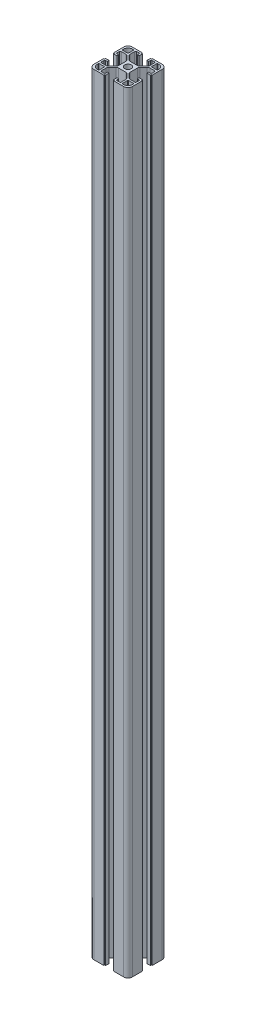
SolidWorks part; units mm, degrees
ref_plane "Front Plane" through (0, 0, 0) normal (0, 0, 1) x (1, 0, 0)
ref_plane "Top Plane" through (0, 0, 0) normal (0, 1, 0) x (1, 0, 0)
ref_plane "Right Plane" through (0, 0, 0) normal (1, 0, 0) x (0, 0, -1)
sketch "Sketch1" plane through (0, 0, 0) normal (0, 1, 0) x (1, 0, 0)
  line L0 (84.1702, 31.7204) -> (84.1702, 42.1204)
  line L1 (44.1702, 62.7204) -> (44.1702, 52.3204)
  line L2 (48.6702, 27.2204) -> (59.0702, 27.2204)
  line L3 (79.6702, 67.2204) -> (69.4702, 67.2204)
  line L4 (84.1702, 52.3204) -> (84.1702, 62.7204)
  line L5 (58.8702, 67.2204) -> (48.6702, 67.2204)
  line L6 (44.1702, 42.1204) -> (44.1702, 31.7204)
  line L7 (69.2702, 27.2204) -> (79.6702, 27.2204)
  line L8 (48.6702, 27.2204) -> (59.0702, 27.2204)
  line L9 (44.1702, 42.1204) -> (44.1702, 31.7204)
  line L10 (44.1702, 42.1204) -> (44.7702, 42.1204)
  line L11 (44.9702, 42.3204) -> (44.9702, 42.9204)
  line L12 (48.6702, 43.1204) -> (45.1702, 43.1204)
  line L13 (48.6702, 41.3204) -> (48.6702, 43.1204)
  line L14 (46.9702, 41.3204) -> (48.6702, 41.3204)
  line L15 (45.9702, 37.9704) -> (45.9702, 40.3204)
  line L16 (51.6169, 36.9704) -> (46.9702, 36.9704)
  line L17 (57.2915, 41.4024) -> (53.7382, 37.8491)
  line L18 (58.1702, 50.9171) -> (58.1702, 43.5237)
  line L19 (53.7382, 56.5917) -> (57.2915, 53.0384)
  line L20 (46.9702, 57.4704) -> (51.6169, 57.4704)
  line L21 (45.9702, 54.1204) -> (45.9702, 56.4704)
  line L22 (48.6702, 53.1204) -> (46.9702, 53.1204)
  line L23 (48.6702, 51.3204) -> (48.6702, 53.1204)
  line L24 (45.1702, 51.3204) -> (48.6702, 51.3204)
  line L25 (44.9702, 51.5204) -> (44.9702, 52.1204)
  line L26 (44.7702, 52.3204) -> (44.1702, 52.3204)
  line L27 (44.1702, 62.7204) -> (44.1702, 52.3204)
  line L28 (58.8702, 67.2204) -> (48.6702, 67.2204)
  line L29 (59.0702, 67.0204) -> (59.0702, 66.6204)
  line L30 (59.2702, 66.4204) -> (59.8702, 66.4204)
  line L31 (60.0702, 62.7204) -> (60.0702, 66.2204)
  line L32 (58.2702, 62.7204) -> (60.0702, 62.7204)
  line L33 (58.2702, 64.4204) -> (58.2702, 62.7204)
  line L34 (54.9202, 65.4204) -> (57.2702, 65.4204)
  line L35 (53.9202, 59.7737) -> (53.9202, 64.4204)
  line L36 (58.3522, 54.0991) -> (54.7989, 57.6524)
  line L37 (67.8669, 53.2204) -> (60.4735, 53.2204)
  line L38 (73.5415, 57.6524) -> (69.9882, 54.0991)
  line L39 (74.4202, 64.4204) -> (74.4202, 59.7737)
  line L40 (71.0702, 65.4204) -> (73.4202, 65.4204)
  line L41 (70.0702, 62.7204) -> (70.0702, 64.4204)
  line L42 (68.2702, 62.7204) -> (70.0702, 62.7204)
  line L43 (68.2702, 66.2204) -> (68.2702, 62.7204)
  line L44 (68.4702, 66.4204) -> (69.0702, 66.4204)
  line L45 (69.2702, 66.6204) -> (69.2702, 67.0204)
  line L46 (79.6702, 67.2204) -> (69.4702, 67.2204)
  line L47 (84.1702, 52.3204) -> (84.1702, 62.7204)
  line L48 (84.1702, 52.3204) -> (83.5702, 52.3204)
  line L49 (83.3702, 52.1204) -> (83.3702, 51.5204)
  line L50 (79.6702, 51.3204) -> (83.1702, 51.3204)
  line L51 (79.6702, 53.1204) -> (79.6702, 51.3204)
  line L52 (81.3702, 53.1204) -> (79.6702, 53.1204)
  line L53 (82.3702, 56.4704) -> (82.3702, 54.1204)
  line L54 (76.7235, 57.4704) -> (81.3702, 57.4704)
  line L55 (71.0489, 53.0384) -> (74.6022, 56.5917)
  line L56 (70.1702, 43.5237) -> (70.1702, 50.9171)
  line L57 (74.6022, 37.8491) -> (71.0489, 41.4024)
  line L58 (81.3702, 36.9704) -> (76.7235, 36.9704)
  line L59 (82.3702, 40.3204) -> (82.3702, 37.9704)
  line L60 (79.6702, 41.3204) -> (81.3702, 41.3204)
  line L61 (79.6702, 43.1204) -> (79.6702, 41.3204)
  line L62 (83.1702, 43.1204) -> (79.6702, 43.1204)
  line L63 (83.3702, 42.9204) -> (83.3702, 42.3204)
  line L64 (83.5702, 42.1204) -> (84.1702, 42.1204)
  line L65 (84.1702, 31.7204) -> (84.1702, 42.1204)
  line L66 (69.2702, 27.2204) -> (79.6702, 27.2204)
  line L67 (69.2702, 27.2204) -> (69.2702, 27.8204)
  line L68 (69.0702, 28.0204) -> (68.4702, 28.0204)
  line L69 (68.2702, 31.7204) -> (68.2702, 28.2204)
  line L70 (70.0702, 31.7204) -> (68.2702, 31.7204)
  line L71 (70.0702, 30.0204) -> (70.0702, 31.7204)
  line L72 (73.4202, 29.0204) -> (71.0702, 29.0204)
  line L73 (74.4202, 34.6671) -> (74.4202, 30.0204)
  line L74 (69.9882, 40.3417) -> (73.5415, 36.7884)
  line L75 (60.4735, 41.2204) -> (67.8669, 41.2204)
  line L76 (54.7989, 36.7884) -> (58.3522, 40.3417)
  line L77 (53.9202, 30.0204) -> (53.9202, 34.6671)
  line L78 (57.2702, 29.0204) -> (54.9202, 29.0204)
  line L79 (58.2702, 31.7204) -> (58.2702, 30.0204)
  line L80 (60.0702, 31.7204) -> (58.2702, 31.7204)
  line L81 (60.0702, 28.2204) -> (60.0702, 31.7204)
  line L82 (59.8702, 28.0204) -> (59.2702, 28.0204)
  line L83 (59.0702, 27.8204) -> (59.0702, 27.2204)
  line L84 (82.3702, 34.6704) -> (82.3702, 33.5204)
  line L85 (76.7202, 35.1704) -> (81.8702, 35.1704)
  line L86 (76.2202, 29.5204) -> (76.2202, 34.6704)
  line L87 (77.8702, 29.0204) -> (76.7202, 29.0204)
  line L88 (51.6202, 29.0204) -> (50.4702, 29.0204)
  line L89 (52.1202, 34.6704) -> (52.1202, 29.5204)
  line L90 (46.4702, 35.1704) -> (51.6202, 35.1704)
  line L91 (45.9702, 33.5204) -> (45.9702, 34.6704)
  line L92 (45.9702, 59.7704) -> (45.9702, 60.9204)
  line L93 (51.6202, 59.2704) -> (46.4702, 59.2704)
  line L94 (52.1202, 64.9204) -> (52.1202, 59.7704)
  line L95 (50.4702, 65.4204) -> (51.6202, 65.4204)
  line L96 (76.7202, 65.4204) -> (77.8702, 65.4204)
  line L97 (76.2202, 59.7704) -> (76.2202, 64.9204)
  line L98 (81.8702, 59.2704) -> (76.7202, 59.2704)
  line L99 (82.3702, 60.9204) -> (82.3702, 59.7704)
  line L100 (71.0702, 65.4204) -> (73.4202, 65.4204)
  line L101 (70.0702, 62.7204) -> (70.0702, 64.4204)
  line L102 (68.2702, 62.7204) -> (70.0702, 62.7204)
  line L103 (68.2702, 66.2204) -> (68.2702, 62.7204)
  line L104 (60.0702, 62.7204) -> (60.0702, 66.2204)
  line L105 (58.2702, 62.7204) -> (60.0702, 62.7204)
  line L106 (58.2702, 64.4204) -> (58.2702, 62.7204)
  line L107 (54.9202, 65.4204) -> (57.2702, 65.4204)
  line L108 (53.9202, 59.7737) -> (53.9202, 64.4204)
  line L109 (58.3522, 54.0991) -> (54.7989, 57.6524)
  line L110 (67.8669, 53.2204) -> (60.4735, 53.2204)
  line L111 (73.5415, 57.6524) -> (69.9882, 54.0991)
  line L112 (74.4202, 64.4204) -> (74.4202, 59.7737)
  line L113 (59.2702, 66.4204) -> (59.8702, 66.4204)
  line L114 (59.0702, 67.0204) -> (59.0702, 66.6204)
  line L115 (69.2702, 66.6204) -> (69.2702, 67.0204)
  line L116 (68.4702, 66.4204) -> (69.0702, 66.4204)
  line L117 (82.3702, 40.3204) -> (82.3702, 37.9704)
  line L118 (79.6702, 41.3204) -> (81.3702, 41.3204)
  line L119 (79.6702, 43.1204) -> (79.6702, 41.3204)
  line L120 (83.1702, 43.1204) -> (79.6702, 43.1204)
  line L121 (79.6702, 51.3204) -> (83.1702, 51.3204)
  line L122 (79.6702, 53.1204) -> (79.6702, 51.3204)
  line L123 (81.3702, 53.1204) -> (79.6702, 53.1204)
  line L124 (82.3702, 56.4704) -> (82.3702, 54.1204)
  line L125 (76.7235, 57.4704) -> (81.3702, 57.4704)
  line L126 (71.0489, 53.0384) -> (74.6022, 56.5917)
  line L127 (70.1702, 43.5237) -> (70.1702, 50.9171)
  line L128 (74.6022, 37.8491) -> (71.0489, 41.4024)
  line L129 (81.3702, 36.9704) -> (76.7235, 36.9704)
  line L130 (45.9702, 54.1204) -> (45.9702, 56.4704)
  line L131 (48.6702, 53.1204) -> (46.9702, 53.1204)
  line L132 (48.6702, 51.3204) -> (48.6702, 53.1204)
  line L133 (45.1702, 51.3204) -> (48.6702, 51.3204)
  line L134 (48.6702, 43.1204) -> (45.1702, 43.1204)
  line L135 (48.6702, 41.3204) -> (48.6702, 43.1204)
  line L136 (46.9702, 41.3204) -> (48.6702, 41.3204)
  line L137 (45.9702, 37.9704) -> (45.9702, 40.3204)
  line L138 (51.6169, 36.9704) -> (46.9702, 36.9704)
  line L139 (57.2915, 41.4024) -> (53.7382, 37.8491)
  line L140 (58.1702, 50.9171) -> (58.1702, 43.5237)
  line L141 (53.7382, 56.5917) -> (57.2915, 53.0384)
  line L142 (46.9702, 57.4704) -> (51.6169, 57.4704)
  line L143 (57.2702, 29.0204) -> (54.9202, 29.0204)
  line L144 (58.2702, 31.7204) -> (58.2702, 30.0204)
  line L145 (60.0702, 31.7204) -> (58.2702, 31.7204)
  line L146 (60.0702, 28.2204) -> (60.0702, 31.7204)
  line L147 (68.2702, 31.7204) -> (68.2702, 28.2204)
  line L148 (70.0702, 31.7204) -> (68.2702, 31.7204)
  line L149 (70.0702, 30.0204) -> (70.0702, 31.7204)
  line L150 (73.4202, 29.0204) -> (71.0702, 29.0204)
  line L151 (74.4202, 34.6671) -> (74.4202, 30.0204)
  line L152 (69.9882, 40.3417) -> (73.5415, 36.7884)
  line L153 (60.4735, 41.2204) -> (67.8669, 41.2204)
  line L154 (54.7989, 36.7884) -> (58.3522, 40.3417)
  line L155 (53.9202, 30.0204) -> (53.9202, 34.6671)
  line L156 (69.0702, 28.0204) -> (68.4702, 28.0204)
  line L157 (69.2702, 27.2204) -> (69.2702, 27.8204)
  line L158 (59.0702, 27.8204) -> (59.0702, 27.2204)
  line L159 (59.8702, 28.0204) -> (59.2702, 28.0204)
  line L160 (44.9702, 42.3204) -> (44.9702, 42.9204)
  line L161 (44.1702, 42.1204) -> (44.7702, 42.1204)
  line L162 (44.7702, 52.3204) -> (44.1702, 52.3204)
  line L163 (44.9702, 51.5204) -> (44.9702, 52.1204)
  line L164 (83.3702, 52.1204) -> (83.3702, 51.5204)
  line L165 (84.1702, 52.3204) -> (83.5702, 52.3204)
  line L166 (83.5702, 42.1204) -> (84.1702, 42.1204)
  line L167 (83.3702, 42.9204) -> (83.3702, 42.3204)
  line L168 (76.2202, 59.7704) -> (76.2202, 64.9204)
  line L169 (81.8702, 59.2704) -> (76.7202, 59.2704)
  line L170 (82.3702, 60.9204) -> (82.3702, 59.7704)
  line L171 (76.7202, 65.4204) -> (77.8702, 65.4204)
  line L172 (51.6202, 59.2704) -> (46.4702, 59.2704)
  line L173 (52.1202, 64.9204) -> (52.1202, 59.7704)
  line L174 (50.4702, 65.4204) -> (51.6202, 65.4204)
  line L175 (45.9702, 59.7704) -> (45.9702, 60.9204)
  line L176 (52.1202, 34.6704) -> (52.1202, 29.5204)
  line L177 (46.4702, 35.1704) -> (51.6202, 35.1704)
  line L178 (45.9702, 33.5204) -> (45.9702, 34.6704)
  line L179 (51.6202, 29.0204) -> (50.4702, 29.0204)
  line L180 (76.7202, 35.1704) -> (81.8702, 35.1704)
  line L181 (76.2202, 29.5204) -> (76.2202, 34.6704)
  line L182 (77.8702, 29.0204) -> (76.7202, 29.0204)
  line L183 (82.3702, 34.6704) -> (82.3702, 33.5204)
  arc A0 (60.7702, 47.2204) -> (67.5702, 47.2204) centre (64.1702, 47.2204) ccw
  arc A1 (44.1702, 31.7204) -> (48.6702, 27.2204) centre (48.6702, 31.7204) ccw
  arc A2 (44.7702, 42.1204) -> (44.9702, 42.3204) centre (44.7702, 42.3204) ccw
  arc A3 (45.1702, 43.1204) -> (44.9702, 42.9204) centre (45.1702, 42.9204) ccw
  arc A4 (46.9702, 41.3204) -> (45.9702, 40.3204) centre (46.9702, 40.3204) ccw
  arc A5 (45.9702, 37.9704) -> (46.9702, 36.9704) centre (46.9702, 37.9704) ccw
  arc A6 (51.6169, 36.9704) -> (53.7382, 37.8491) centre (51.6169, 39.9704) ccw
  arc A7 (57.2915, 41.4024) -> (58.1702, 43.5237) centre (55.1702, 43.5237) ccw
  arc A8 (58.1702, 50.9171) -> (57.2915, 53.0384) centre (55.1702, 50.9171) ccw
  arc A9 (53.7382, 56.5917) -> (51.6169, 57.4704) centre (51.6169, 54.4704) ccw
  arc A10 (46.9702, 57.4704) -> (45.9702, 56.4704) centre (46.9702, 56.4704) ccw
  arc A11 (45.9702, 54.1204) -> (46.9702, 53.1204) centre (46.9702, 54.1204) ccw
  arc A12 (44.9702, 51.5204) -> (45.1702, 51.3204) centre (45.1702, 51.5204) ccw
  arc A13 (44.9702, 52.1204) -> (44.7702, 52.3204) centre (44.7702, 52.1204) ccw
  arc A14 (48.6702, 67.2204) -> (44.1702, 62.7204) centre (48.6702, 62.7204) ccw
  arc A15 (59.0702, 67.0204) -> (58.8702, 67.2204) centre (58.8702, 67.0204) ccw
  arc A16 (59.0702, 66.6204) -> (59.2702, 66.4204) centre (59.2702, 66.6204) ccw
  arc A17 (60.0702, 66.2204) -> (59.8702, 66.4204) centre (59.8702, 66.2204) ccw
  arc A18 (58.2702, 64.4204) -> (57.2702, 65.4204) centre (57.2702, 64.4204) ccw
  arc A19 (54.9202, 65.4204) -> (53.9202, 64.4204) centre (54.9202, 64.4204) ccw
  arc A20 (53.9202, 59.7737) -> (54.7989, 57.6524) centre (56.9202, 59.7737) ccw
  arc A21 (58.3522, 54.0991) -> (60.4735, 53.2204) centre (60.4735, 56.2204) ccw
  arc A22 (67.8669, 53.2204) -> (69.9882, 54.0991) centre (67.8669, 56.2204) ccw
  arc A23 (73.5415, 57.6524) -> (74.4202, 59.7737) centre (71.4202, 59.7737) ccw
  arc A24 (74.4202, 64.4204) -> (73.4202, 65.4204) centre (73.4202, 64.4204) ccw
  arc A25 (71.0702, 65.4204) -> (70.0702, 64.4204) centre (71.0702, 64.4204) ccw
  arc A26 (68.4702, 66.4204) -> (68.2702, 66.2204) centre (68.4702, 66.2204) ccw
  arc A27 (69.0702, 66.4204) -> (69.2702, 66.6204) centre (69.0702, 66.6204) ccw
  arc A28 (69.4702, 67.2204) -> (69.2702, 67.0204) centre (69.4702, 67.0204) ccw
  arc A29 (84.1702, 62.7204) -> (79.6702, 67.2204) centre (79.6702, 62.7204) ccw
  arc A30 (83.5702, 52.3204) -> (83.3702, 52.1204) centre (83.5702, 52.1204) ccw
  arc A31 (83.1702, 51.3204) -> (83.3702, 51.5204) centre (83.1702, 51.5204) ccw
  arc A32 (81.3702, 53.1204) -> (82.3702, 54.1204) centre (81.3702, 54.1204) ccw
  arc A33 (82.3702, 56.4704) -> (81.3702, 57.4704) centre (81.3702, 56.4704) ccw
  arc A34 (76.7235, 57.4704) -> (74.6022, 56.5917) centre (76.7235, 54.4704) ccw
  arc A35 (71.0489, 53.0384) -> (70.1702, 50.9171) centre (73.1702, 50.9171) ccw
  arc A36 (70.1702, 43.5237) -> (71.0489, 41.4024) centre (73.1702, 43.5237) ccw
  arc A37 (74.6022, 37.8491) -> (76.7235, 36.9704) centre (76.7235, 39.9704) ccw
  arc A38 (81.3702, 36.9704) -> (82.3702, 37.9704) centre (81.3702, 37.9704) ccw
  arc A39 (82.3702, 40.3204) -> (81.3702, 41.3204) centre (81.3702, 40.3204) ccw
  arc A40 (83.3702, 42.9204) -> (83.1702, 43.1204) centre (83.1702, 42.9204) ccw
  arc A41 (83.3702, 42.3204) -> (83.5702, 42.1204) centre (83.5702, 42.3204) ccw
  arc A42 (79.6702, 27.2204) -> (84.1702, 31.7204) centre (79.6702, 31.7204) ccw
  arc A43 (69.2702, 27.8204) -> (69.0702, 28.0204) centre (69.0702, 27.8204) ccw
  arc A44 (68.2702, 28.2204) -> (68.4702, 28.0204) centre (68.4702, 28.2204) ccw
  arc A45 (70.0702, 30.0204) -> (71.0702, 29.0204) centre (71.0702, 30.0204) ccw
  arc A46 (73.4202, 29.0204) -> (74.4202, 30.0204) centre (73.4202, 30.0204) ccw
  arc A47 (74.4202, 34.6671) -> (73.5415, 36.7884) centre (71.4202, 34.6671) ccw
  arc A48 (69.9882, 40.3417) -> (67.8669, 41.2204) centre (67.8669, 38.2204) ccw
  arc A49 (60.4735, 41.2204) -> (58.3522, 40.3417) centre (60.4735, 38.2204) ccw
  arc A50 (54.7989, 36.7884) -> (53.9202, 34.6671) centre (56.9202, 34.6671) ccw
  arc A51 (53.9202, 30.0204) -> (54.9202, 29.0204) centre (54.9202, 30.0204) ccw
  arc A52 (57.2702, 29.0204) -> (58.2702, 30.0204) centre (57.2702, 30.0204) ccw
  arc A53 (59.8702, 28.0204) -> (60.0702, 28.2204) centre (59.8702, 28.2204) ccw
  arc A54 (59.2702, 28.0204) -> (59.0702, 27.8204) centre (59.2702, 27.8204) ccw
  arc A55 (82.3702, 34.6704) -> (81.8702, 35.1704) centre (81.8702, 34.6704) ccw
  arc A56 (76.7202, 35.1704) -> (76.2202, 34.6704) centre (76.7202, 34.6704) ccw
  arc A57 (76.2202, 29.5204) -> (76.7202, 29.0204) centre (76.7202, 29.5204) ccw
  arc A58 (77.8702, 29.0204) -> (82.3702, 33.5204) centre (77.8702, 33.5204) ccw
  arc A59 (51.6202, 29.0204) -> (52.1202, 29.5204) centre (51.6202, 29.5204) ccw
  arc A60 (52.1202, 34.6704) -> (51.6202, 35.1704) centre (51.6202, 34.6704) ccw
  arc A61 (46.4702, 35.1704) -> (45.9702, 34.6704) centre (46.4702, 34.6704) ccw
  arc A62 (45.9702, 33.5204) -> (50.4702, 29.0204) centre (50.4702, 33.5204) ccw
  arc A63 (45.9702, 59.7704) -> (46.4702, 59.2704) centre (46.4702, 59.7704) ccw
  arc A64 (51.6202, 59.2704) -> (52.1202, 59.7704) centre (51.6202, 59.7704) ccw
  arc A65 (52.1202, 64.9204) -> (51.6202, 65.4204) centre (51.6202, 64.9204) ccw
  arc A66 (50.4702, 65.4204) -> (45.9702, 60.9204) centre (50.4702, 60.9204) ccw
  arc A67 (76.7202, 65.4204) -> (76.2202, 64.9204) centre (76.7202, 64.9204) ccw
  arc A68 (76.2202, 59.7704) -> (76.7202, 59.2704) centre (76.7202, 59.7704) ccw
  arc A69 (81.8702, 59.2704) -> (82.3702, 59.7704) centre (81.8702, 59.7704) ccw
  arc A70 (82.3702, 60.9204) -> (77.8702, 65.4204) centre (77.8702, 60.9204) ccw
  arc A71 (67.5702, 47.2204) -> (60.7702, 47.2204) centre (64.1702, 47.2204) ccw
  arc A72 (60.7702, 47.2204) -> (67.5702, 47.2204) centre (64.1702, 47.2204) ccw
  arc A73 (67.5702, 47.2204) -> (60.7702, 47.2204) centre (64.1702, 47.2204) ccw
  arc A74 (71.0702, 65.4204) -> (70.0702, 64.4204) centre (71.0702, 64.4204) ccw
  arc A75 (54.9202, 65.4204) -> (53.9202, 64.4204) centre (54.9202, 64.4204) ccw
  arc A76 (58.2702, 64.4204) -> (57.2702, 65.4204) centre (57.2702, 64.4204) ccw
  arc A77 (74.4202, 64.4204) -> (73.4202, 65.4204) centre (73.4202, 64.4204) ccw
  arc A78 (60.0702, 66.2204) -> (59.8702, 66.4204) centre (59.8702, 66.2204) ccw
  arc A79 (68.4702, 66.4204) -> (68.2702, 66.2204) centre (68.4702, 66.2204) ccw
  arc A80 (69.4702, 67.2204) -> (69.2702, 67.0204) centre (69.4702, 67.0204) ccw
  arc A81 (69.0702, 66.4204) -> (69.2702, 66.6204) centre (69.0702, 66.6204) ccw
  arc A82 (59.0702, 67.0204) -> (58.8702, 67.2204) centre (58.8702, 67.0204) ccw
  arc A83 (59.0702, 66.6204) -> (59.2702, 66.4204) centre (59.2702, 66.6204) ccw
  arc A84 (82.3702, 40.3204) -> (81.3702, 41.3204) centre (81.3702, 40.3204) ccw
  arc A85 (82.3702, 56.4704) -> (81.3702, 57.4704) centre (81.3702, 56.4704) ccw
  arc A86 (81.3702, 53.1204) -> (82.3702, 54.1204) centre (81.3702, 54.1204) ccw
  arc A87 (81.3702, 36.9704) -> (82.3702, 37.9704) centre (81.3702, 37.9704) ccw
  arc A88 (57.2702, 29.0204) -> (58.2702, 30.0204) centre (57.2702, 30.0204) ccw
  arc A89 (73.4202, 29.0204) -> (74.4202, 30.0204) centre (73.4202, 30.0204) ccw
  arc A90 (70.0702, 30.0204) -> (71.0702, 29.0204) centre (71.0702, 30.0204) ccw
  arc A91 (53.9202, 30.0204) -> (54.9202, 29.0204) centre (54.9202, 30.0204) ccw
  arc A92 (45.9702, 54.1204) -> (46.9702, 53.1204) centre (46.9702, 54.1204) ccw
  arc A93 (45.9702, 37.9704) -> (46.9702, 36.9704) centre (46.9702, 37.9704) ccw
  arc A94 (46.9702, 41.3204) -> (45.9702, 40.3204) centre (46.9702, 40.3204) ccw
  arc A95 (46.9702, 57.4704) -> (45.9702, 56.4704) centre (46.9702, 56.4704) ccw
  arc A96 (83.1702, 51.3204) -> (83.3702, 51.5204) centre (83.1702, 51.5204) ccw
  arc A97 (83.3702, 42.9204) -> (83.1702, 43.1204) centre (83.1702, 42.9204) ccw
  arc A98 (83.3702, 42.3204) -> (83.5702, 42.1204) centre (83.5702, 42.3204) ccw
  arc A99 (83.5702, 52.3204) -> (83.3702, 52.1204) centre (83.5702, 52.1204) ccw
  arc A100 (68.2702, 28.2204) -> (68.4702, 28.0204) centre (68.4702, 28.2204) ccw
  arc A101 (59.8702, 28.0204) -> (60.0702, 28.2204) centre (59.8702, 28.2204) ccw
  arc A102 (59.2702, 28.0204) -> (59.0702, 27.8204) centre (59.2702, 27.8204) ccw
  arc A103 (69.2702, 27.8204) -> (69.0702, 28.0204) centre (69.0702, 27.8204) ccw
  arc A104 (45.1702, 43.1204) -> (44.9702, 42.9204) centre (45.1702, 42.9204) ccw
  arc A105 (44.9702, 51.5204) -> (45.1702, 51.3204) centre (45.1702, 51.5204) ccw
  arc A106 (44.9702, 52.1204) -> (44.7702, 52.3204) centre (44.7702, 52.1204) ccw
  arc A107 (44.7702, 42.1204) -> (44.9702, 42.3204) centre (44.7702, 42.3204) ccw
  arc A108 (44.1702, 31.7204) -> (48.6702, 27.2204) centre (48.6702, 31.7204) ccw
  arc A109 (79.6702, 27.2204) -> (84.1702, 31.7204) centre (79.6702, 31.7204) ccw
  arc A110 (48.6702, 67.2204) -> (44.1702, 62.7204) centre (48.6702, 62.7204) ccw
  arc A111 (84.1702, 62.7204) -> (79.6702, 67.2204) centre (79.6702, 62.7204) ccw
  arc A112 (82.3702, 60.9204) -> (77.8702, 65.4204) centre (77.8702, 60.9204) ccw
  arc A113 (81.8702, 59.2704) -> (82.3702, 59.7704) centre (81.8702, 59.7704) ccw
  arc A114 (76.7202, 65.4204) -> (76.2202, 64.9204) centre (76.7202, 64.9204) ccw
  arc A115 (76.2202, 59.7704) -> (76.7202, 59.2704) centre (76.7202, 59.7704) ccw
  arc A116 (50.4702, 65.4204) -> (45.9702, 60.9204) centre (50.4702, 60.9204) ccw
  arc A117 (45.9702, 33.5204) -> (50.4702, 29.0204) centre (50.4702, 33.5204) ccw
  arc A118 (77.8702, 29.0204) -> (82.3702, 33.5204) centre (77.8702, 33.5204) ccw
  arc A119 (76.2202, 29.5204) -> (76.7202, 29.0204) centre (76.7202, 29.5204) ccw
  arc A120 (82.3702, 34.6704) -> (81.8702, 35.1704) centre (81.8702, 34.6704) ccw
  arc A121 (76.7202, 35.1704) -> (76.2202, 34.6704) centre (76.7202, 34.6704) ccw
  arc A122 (46.4702, 35.1704) -> (45.9702, 34.6704) centre (46.4702, 34.6704) ccw
  arc A123 (51.6202, 29.0204) -> (52.1202, 29.5204) centre (51.6202, 29.5204) ccw
  arc A124 (52.1202, 34.6704) -> (51.6202, 35.1704) centre (51.6202, 34.6704) ccw
  arc A125 (52.1202, 64.9204) -> (51.6202, 65.4204) centre (51.6202, 64.9204) ccw
  arc A126 (45.9702, 59.7704) -> (46.4702, 59.2704) centre (46.4702, 59.7704) ccw
  arc A127 (51.6202, 59.2704) -> (52.1202, 59.7704) centre (51.6202, 59.7704) ccw
  arc A128 (74.6022, 37.8491) -> (76.7235, 36.9704) centre (76.7235, 39.9704) ccw
  arc A129 (70.1702, 43.5237) -> (71.0489, 41.4024) centre (73.1702, 43.5237) ccw
  arc A130 (74.4202, 34.6671) -> (73.5415, 36.7884) centre (71.4202, 34.6671) ccw
  arc A131 (69.9882, 40.3417) -> (67.8669, 41.2204) centre (67.8669, 38.2204) ccw
  arc A132 (54.7989, 36.7884) -> (53.9202, 34.6671) centre (56.9202, 34.6671) ccw
  arc A133 (60.4735, 41.2204) -> (58.3522, 40.3417) centre (60.4735, 38.2204) ccw
  arc A134 (51.6169, 36.9704) -> (53.7382, 37.8491) centre (51.6169, 39.9704) ccw
  arc A135 (57.2915, 41.4024) -> (58.1702, 43.5237) centre (55.1702, 43.5237) ccw
  arc A136 (58.1702, 50.9171) -> (57.2915, 53.0384) centre (55.1702, 50.9171) ccw
  arc A137 (53.7382, 56.5917) -> (51.6169, 57.4704) centre (51.6169, 54.4704) ccw
  arc A138 (53.9202, 59.7737) -> (54.7989, 57.6524) centre (56.9202, 59.7737) ccw
  arc A139 (58.3522, 54.0991) -> (60.4735, 53.2204) centre (60.4735, 56.2204) ccw
  arc A140 (67.8669, 53.2204) -> (69.9882, 54.0991) centre (67.8669, 56.2204) ccw
  arc A141 (71.0489, 53.0384) -> (70.1702, 50.9171) centre (73.1702, 50.9171) ccw
  arc A142 (76.7235, 57.4704) -> (74.6022, 56.5917) centre (76.7235, 54.4704) ccw
  arc A143 (73.5415, 57.6524) -> (74.4202, 59.7737) centre (71.4202, 59.7737) ccw
extrude "Boss-Extrude1" add sketch "Sketch1" along normal blind 800 contours A54 L82 A53 L81 L80 L79 A52 L78 A51 L77 A50 L76 A49 L75 A48 L74 A47 L73 A46 L72 A45 L71 L70 L69 A44 L68 A43 L67 L7 A42 L0 L64 A41 L63 A40 L62 L61 L60 A39 L59 A38 L58 A37 L57 A36 L56 A35 L55 A34 L54 A33
